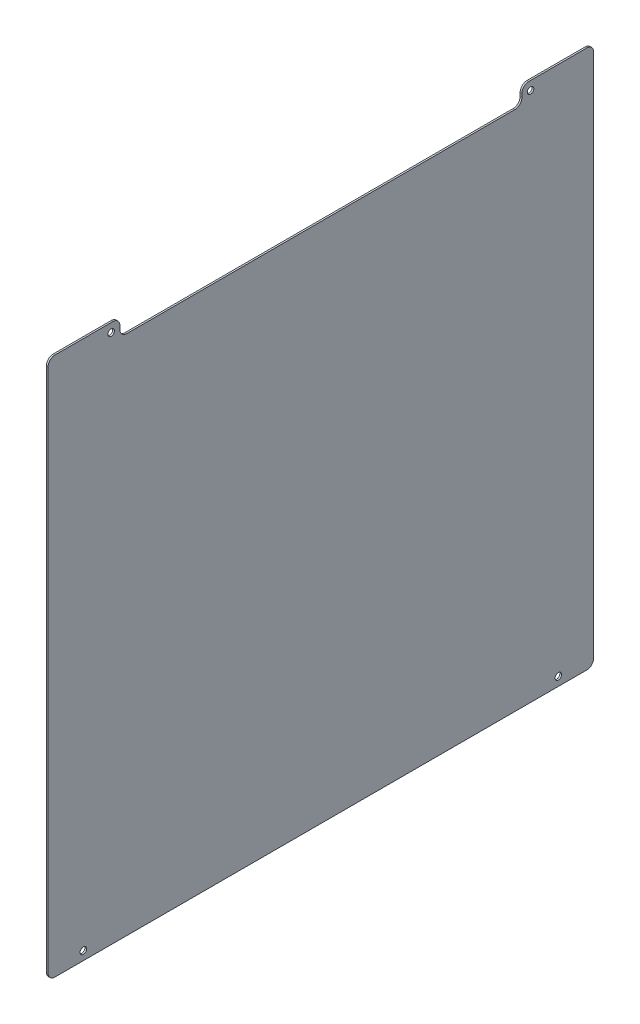
SolidWorks part; units mm, degrees
ref_plane "Front Plane" through (0, 0, 0) normal (0, 0, 1) x (1, 0, 0)
ref_plane "Top Plane" through (0, 0, 0) normal (0, 1, 0) x (1, 0, 0)
ref_plane "Right Plane" through (0, 0, 0) normal (1, 0, 0) x (0, 0, -1)
sketch "Sketch1" plane through (0, 0, 0) normal (1, 0, 0) x (0, 0, -1)
  line L0 (438.6326, 491.49) -> (491.49, 491.49)
  line L1 (6.35, 0) -> (491.49, 0)
  line L2 (0, 6.35) -> (0, 485.14)
  line L3 (6.35, 491.49) -> (59.2074, 491.49)
  line L4 (497.84, 6.35) -> (497.84, 485.14)
  line L6 (65.5574, 485.14) -> (65.5574, 481.965)
  line L7 (71.9074, 475.615) -> (425.9326, 475.615)
  line L8 (432.2826, 485.14) -> (432.2826, 481.965)
  arc A0 (6.35, 0) -> (0, 6.35) centre (6.35, 6.35) cw
  arc A1 (497.84, 6.35) -> (491.49, 0) centre (491.49, 6.35) cw
  arc A2 (497.84, 485.14) -> (491.49, 491.49) centre (491.49, 485.14) ccw
  arc A3 (438.6326, 491.49) -> (432.2826, 485.14) centre (438.6326, 485.14) ccw
  arc A4 (432.2826, 481.965) -> (425.9326, 475.615) centre (425.9326, 481.965) cw
  arc A5 (71.9074, 475.615) -> (65.5574, 481.965) centre (71.9074, 481.965) cw
  arc A6 (65.5574, 485.14) -> (59.2074, 491.49) centre (59.2074, 485.14) ccw
  arc A7 (6.35, 491.49) -> (0, 485.14) centre (6.35, 485.14) ccw
  point P11 (0, 0)
  point P14 (497.84, 0)
  point P17 (497.84, 491.49)
  point P20 (432.2826, 491.49)
  point P23 (432.2826, 475.615)
  point P30 (0, 491.49)
  dimension "D6" = 6.35
  dimension "D1" = 497.84
  dimension "D2" = 491.49
  dimension "D3" = 15.875
  dimension "D4" = 65.5574
  dimension "D5" = 65.5574
extrude "Boss-Extrude1" add sketch "Sketch1" against normal blind 1.5875
hole_wizard "A (0.234) Diameter Hole1" positions "Sketch2" profile "Sketch3" hole size "A" standard "ANSI Inch" end condition through all
sketch "Sketch2" plane through (1.0236, -1353.3618, -2205.8131) normal (1, 0, 0) x (0, 0, -1)
  line L0 (-2205.8131, 1838.5018) -> (-2205.8131, 1359.7118) construction
  line L1 (-1707.9731, 1359.7118) -> (-1707.9731, 1838.5018) construction
  point P0 (-2173.5932, 1361.2993)
  point P3 (-1740.193, 1361.2992)
  point P6 (-1765.593, 1836.9142)
  point P9 (-2148.1932, 1836.9142)
  dimension "D1" = 57.6199
  dimension "D2" = 57.6199
  dimension "D3" = 32.2199
  dimension "D4" = 32.2199
sketch "Sketch3" plane through (1.0236, 7.9375, -32.2199) normal (0, 1, 0) x (0, 0, -1)
  line L0 (0, 0) -> (0, 2.6111)
  line L1 (0, 2.6111) -> (2.9718, 2.6111)
  line L2 (2.9718, 2.6111) -> (2.9718, 0)
  line L3 (2.9718, 0) -> (0, 0)
  line L4 (0, -6.35) -> (0, 107.95) construction
  dimension "Thru Hole Dia." = 5.9436
  dimension "Thru Hole Depth" = 2.6111
